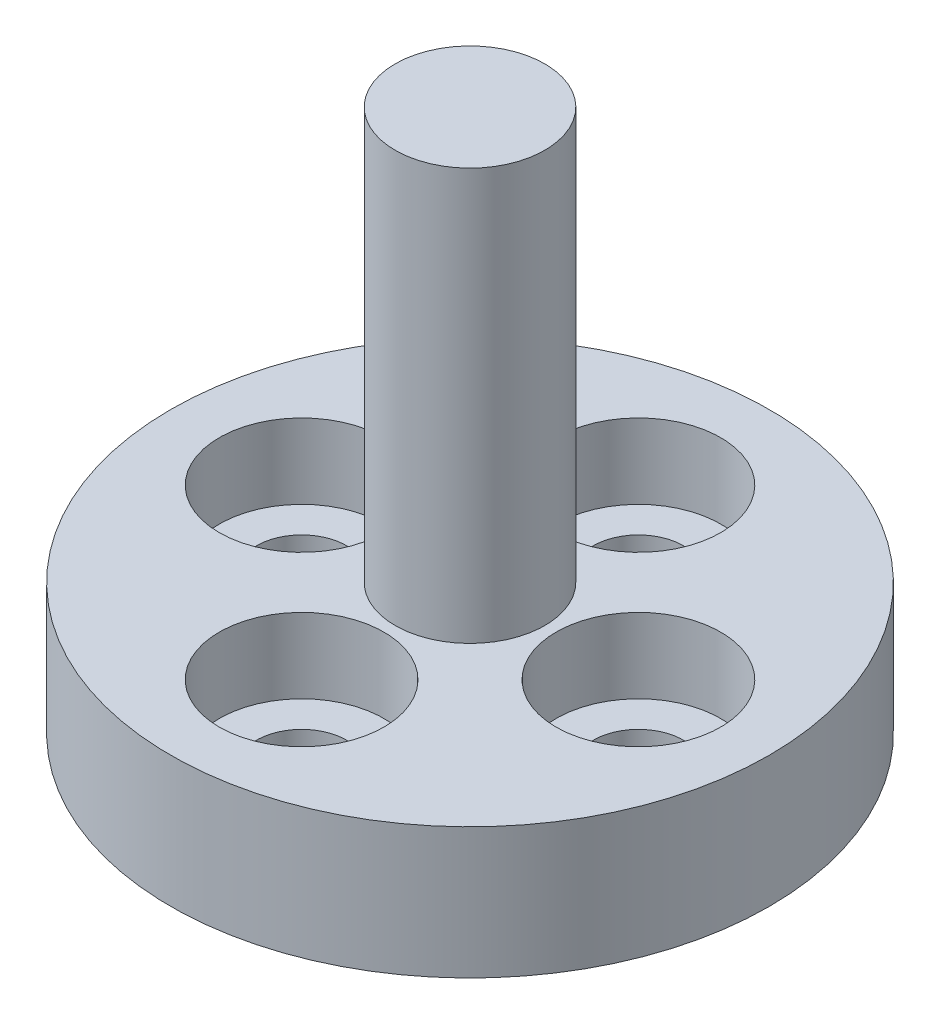
SolidWorks part; units mm, degrees
ref_plane "Front Plane" through (0, 0, 0) normal (0, 0, 1) x (1, 0, 0)
ref_plane "Top Plane" through (0, 0, 0) normal (0, 1, 0) x (1, 0, 0)
ref_plane "Right Plane" through (0, 0, 0) normal (1, 0, 0) x (0, 0, -1)
sketch "Sketch1" plane through (0, 0, 0) normal (0, 0, 1) x (1, 0, 0)
  line L0 (0, 0) -> (8, 0)
  line L1 (8, 0) -> (8, 3.5)
  line L2 (8, 3.5) -> (2, 3.5)
  line L3 (2, 3.5) -> (2, 14.5)
  line L4 (2, 14.5) -> (0, 14.5)
  line L5 (0, 14.5) -> (0, 0)
  dimension "D1" = 8
  dimension "D2" = 14.5
  dimension "D3" = 11
  dimension "D4" = 2
revolve "Revolve1" add sketch "Sketch1" angle 360 about L5
sketch "Sketch2" plane through (0, 3.5, 0) normal (0, 1, 0) x (1, 0, 0)
  circle A0 centre (0, 0) radius 4.5
  dimension "D1" = 9
hole_wizard "CBORE for M2 SHCS1" positions "Sketch3" profile "Sketch4" counterbore size "M2" standard "ANSI Metric" end condition through all
sketch "Sketch3" plane through (0, 3.5, 0) normal (0, 1, 0) x (1, 0, 0)
  circle A0 centre (0, 0) radius 4.5 construction
  point P0 (-4.5, 0)
  point P4 (0, 4.5)
  point P6 (4.5, 0)
  point P8 (0, -4.5)
sketch "Sketch4" plane through (-4.5, 3.5, 0) normal (1, 0, 0) x (0, 0, 1)
  line L0 (0, 0) -> (0, 3.5)
  line L1 (0, 3.5) -> (1.2, 3.5)
  line L3 (1.2, 3.5) -> (1.2, 2)
  line L4 (1.2, 2) -> (2.2, 2)
  line L5 (2.2, 2) -> (2.2, 0)
  line L7 (2.2, 0) -> (0, 0)
  line L11 (0, -6.35) -> (0, 107.95) construction
  dimension "Thru Hole Dia." = 2.4
  dimension "Thru Hole Depth" = 3.5
  dimension "C'Bore Dia." = 4.4
  dimension "C'Bore Depth" = 2
